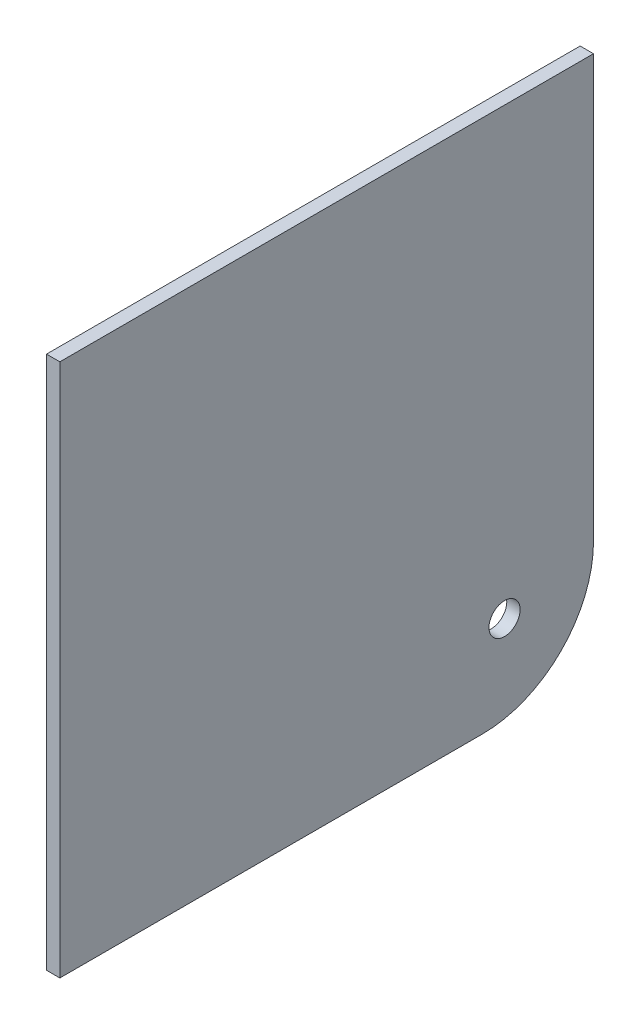
SolidWorks part; units mm, degrees
material "Acrylic (Medium-high impact)"
ref_plane "Front Plane" through (0, 0, 0) normal (0, 0, 1) x (1, 0, 0)
ref_plane "Top Plane" through (0, 0, 0) normal (0, 1, 0) x (1, 0, 0)
ref_plane "Right Plane" through (0, 0, 0) normal (1, 0, 0) x (0, 0, -1)
sketch "Sketch1" plane through (0, 0, 0) normal (1, 0, 0) x (0, 0, -1)
  line L0 (9.8845, -40) -> (60, -40) construction
  line L1 (60, 60) -> (-60, 60)
  line L2 (60, 60) -> (60, -35)
  line L4 (-60, 60) -> (-60, -60)
  line L5 (0, -60) -> (0, 60) construction
  line L6 (60, 0) -> (-60, 0) construction
  line L7 (40, -20.5958) -> (40, -60) construction
  line L8 (35, -60) -> (-60, -60)
  circle A0 centre (40, -40) radius 3.5
  arc A1 (60, -35) -> (35, -60) centre (35, -35) cw
  point P0 (0, 0)
  dimension "D5" = 7
  dimension "D4" = 20
extrude "Boss-Extrude1" add sketch "Sketch1" along normal blind 3
